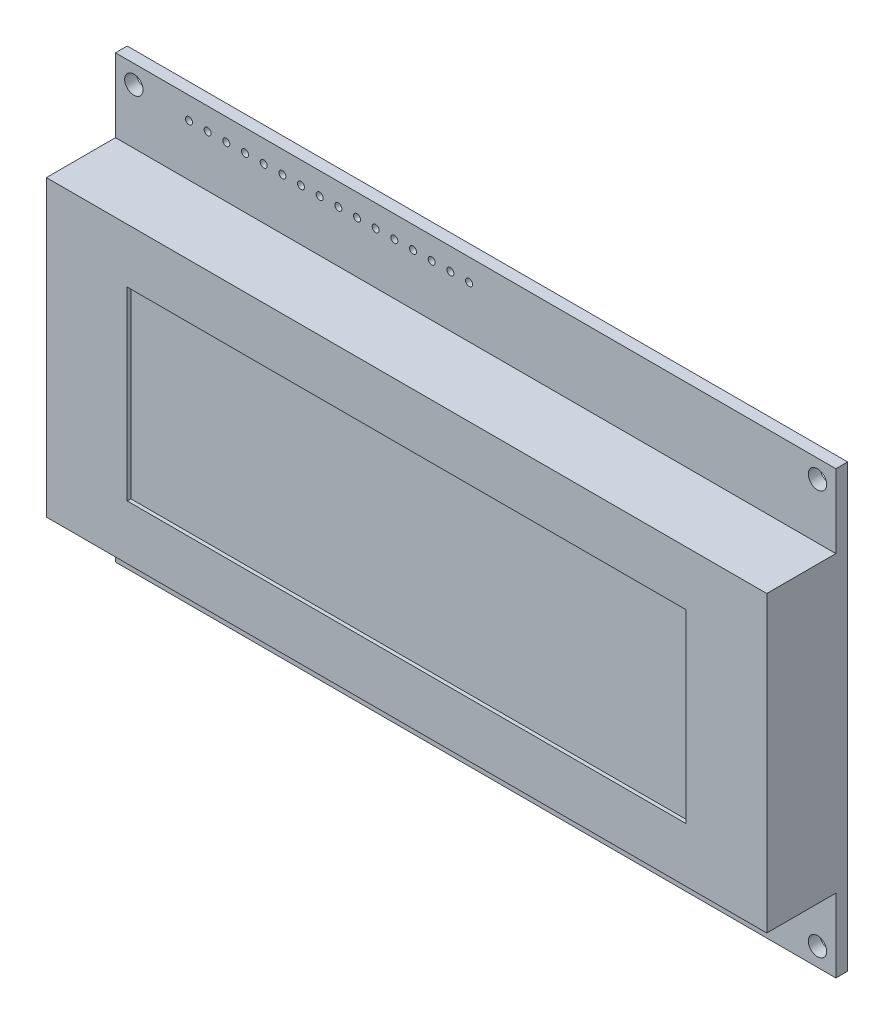
SolidWorks part; units mm, degrees
ref_plane "Front Plane" through (0, 0, 0) normal (0, 0, 1) x (1, 0, 0)
ref_plane "Top Plane" through (0, 0, 0) normal (0, 1, 0) x (1, 0, 0)
ref_plane "Right Plane" through (0, 0, 0) normal (1, 0, 0) x (0, 0, -1)
ref_plane "Plane1" through (0, 0, 11) normal (0, 0, 1) x (1, 0, 0)
sketch "Sketch1" plane through (0, 0, 11) normal (0, 0, 1) x (1, 0, 0)
  line L0 (49, -30) -> (49, 30)
  line L1 (49, 30) -> (-49, 30)
  line L2 (-49, 30) -> (-49, -30)
  line L3 (-49, -30) -> (49, -30)
extrude "Boss-Extrude1" add sketch "Sketch1" against normal blind 11
sketch "Sketch2" plane through (49, 0, 0) normal (1, 0, 0) x (0, 0, -1)
  line L0 (-1.6, -20) -> (-11, -20)
  line L1 (-11, -20) -> (-11, -30)
  line L2 (-11, -30) -> (-1.6, -30)
  line L3 (-1.6, -30) -> (-1.6, -20)
extrude "Cut-Extrude1" cut sketch "Sketch2" against normal through all
sketch "Sketch3" plane through (49, 0, 0) normal (1, 0, 0) x (0, 0, -1)
  line L0 (-11, 20) -> (-1.6, 20)
  line L1 (-1.6, 20) -> (-1.6, 30)
  line L2 (-1.6, 30) -> (-11, 30)
  line L3 (-11, 30) -> (-11, 20)
extrude "Cut-Extrude2" cut sketch "Sketch3" against normal through all
sketch "Sketch4" plane through (0, 0, 0) normal (0, 0, -1) x (-1, 0, 0)
  line L0 (-32.6764, 17.5014) -> (-32.6764, 16.4281)
  line L1 (-32.6764, 16.4281) -> (-36.6119, 16.4281)
  line L2 (-36.6119, 16.4281) -> (-36.6119, 17.5014)
  line L3 (-36.6119, 17.5014) -> (-32.6764, 17.5014)
extrude "Boss-Extrude2" add sketch "Sketch4" along normal blind 3
sketch "Sketch5" plane through (0, 0, 0) normal (0, 0, -1) x (-1, 0, 0)
  line L0 (29.315, -21.1409) -> (29.315, -22.2597)
  line L1 (29.315, -22.2597) -> (26.3, -22.2597)
  line L2 (26.3, -22.2597) -> (26.3, -21.1409)
  line L3 (26.3, -21.1409) -> (29.315, -21.1409)
extrude "Boss-Extrude3" add sketch "Sketch5" along normal blind 3
sketch "Sketch6" plane through (0, 0, 11) normal (0, 0, 1) x (1, 0, 0)
  line L0 (-38, -12.6) -> (38, -12.6)
  line L1 (38, -12.6) -> (38, 12.6)
  line L2 (38, 12.6) -> (-38, 12.6)
  line L3 (-38, 12.6) -> (-38, -12.6)
extrude "Cut-Extrude3" cut sketch "Sketch6" against normal blind 0.5
hole_wizard "Ø2.5 (2.5) Diameter Hole1" positions "Sketch8" profile "Sketch7" hole size "Ø2.5" standard "ANSI Metric"
sketch "Sketch8" plane through (0, 0, 0) normal (0, 0, -1) x (-1, 0, 0)
  point P0 (46.5, -27.5)
  point P1 (-46.5, -27.5)
  point P2 (-46.5, 27.5)
  point P3 (46.5, 27.5)
sketch "Sketch7" plane through (-46.5, -27.5, 0) normal (1, 0, 0) x (0, 1, 0)
  line L0 (0, 0) -> (0, 11)
  line L1 (0, 11) -> (1.25, 11)
  line L2 (1.25, 11) -> (1.25, 0)
  line L5 (1.25, 0) -> (0, 0)
  line L11 (0, -6.35) -> (0, 107.95) construction
  dimension "Thru Hole Dia." = 2.5
  dimension "Thru Hole Depth" = 11
hole_wizard "Ø0.95 (0.95) Diameter Hole1" positions "Sketch10" profile "Sketch9" hole size "Ø0.95" standard "ANSI Metric"
sketch "Sketch10" plane through (0, 0, 0) normal (0, 0, -1) x (-1, 0, 0)
  point P0 (0.9, 27)
  point P1 (3.44, 27)
  point P2 (5.98, 27)
  point P3 (8.52, 27)
  point P4 (11.06, 27)
  point P5 (13.6, 27)
  point P6 (16.14, 27)
  point P7 (18.68, 27)
  point P8 (21.22, 27)
  point P9 (23.76, 27)
  point P10 (26.3, 27)
  point P11 (28.84, 27)
  point P12 (31.38, 27)
  point P13 (33.92, 27)
  point P14 (36.46, 27)
  point P15 (39, 27)
sketch "Sketch9" plane through (-0.9, 27, 0) normal (1, 0, 0) x (0, 1, 0)
  line L0 (0, 0) -> (0, 11)
  line L1 (0, 11) -> (0.475, 11)
  line L2 (0.475, 11) -> (0.475, 0)
  line L5 (0.475, 0) -> (0, 0)
  line L11 (0, -6.35) -> (0, 107.95) construction
  dimension "Thru Hole Dia." = 0.95
  dimension "Thru Hole Depth" = 11
